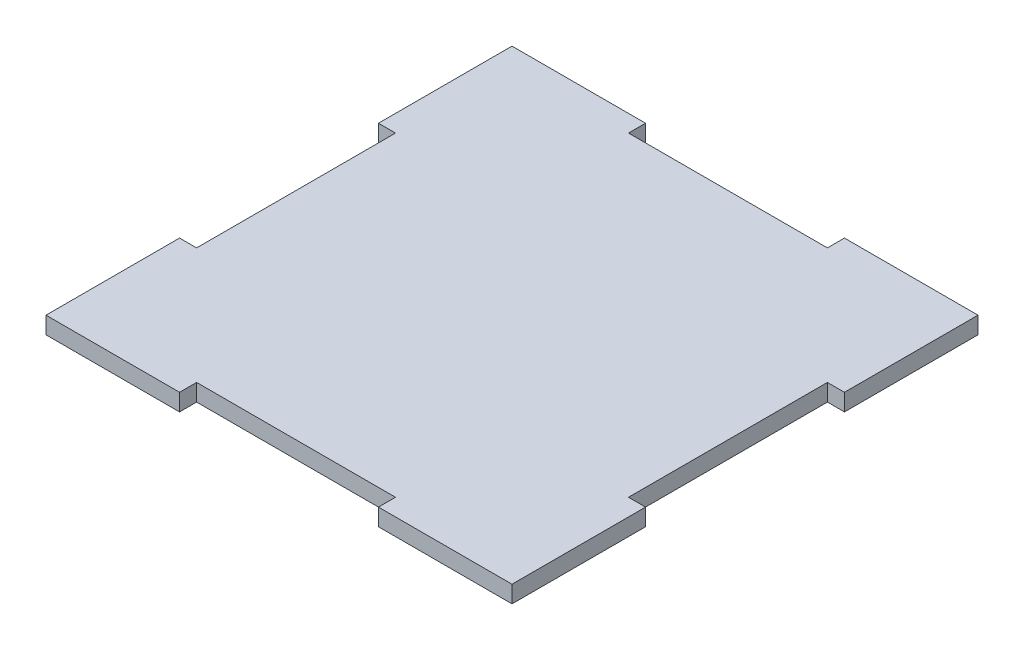
SolidWorks part; units mm, degrees
ref_plane "Front Plane" through (0, 0, 0) normal (0, 0, 1) x (1, 0, 0)
ref_plane "Top Plane" through (0, 0, 0) normal (0, 1, 0) x (1, 0, 0)
ref_plane "Right Plane" through (0, 0, 0) normal (1, 0, 0) x (0, 0, -1)
sketch "Sketch1" plane through (0, 0, 0) normal (0, 1, 0) x (1, 0, 0)
  line L0 (0, 38) -> (0, -38) construction
  line L1 (-41, -41) -> (-17.5, -41)
  line L2 (-41, -41) -> (-41, -17.5)
  line L3 (-41, 41) -> (-17.5, 41)
  line L4 (41, -41) -> (41, -17.5)
  line L5 (-41, -41) -> (41, 41) construction
  line L6 (-41, 41) -> (41, -41) construction
  line L11 (-41, 17.5) -> (-38, 17.5)
  line L12 (-38, 17.5) -> (-38, -17.5)
  line L13 (-35, 0) -> (38, 0) construction
  line L26 (17.5, 41) -> (41, 41)
  line L27 (41, 17.5) -> (41, 41)
  line L28 (17.5, -41) -> (41, -41)
  line L29 (-41, 17.5) -> (-41, 41)
  line L30 (-38, -17.5) -> (-41, -17.5)
  line L31 (-17.5, 41) -> (-17.5, 38)
  line L32 (-17.5, 38) -> (17.5, 38)
  line L33 (17.5, 38) -> (17.5, 41)
  line L34 (41, 17.5) -> (38, 17.5)
  line L35 (38, 17.5) -> (38, -17.5)
  line L36 (38, -17.5) -> (41, -17.5)
  line L37 (17.5, -41) -> (17.5, -38)
  line L38 (17.5, -38) -> (-17.5, -38)
  line L39 (-17.5, -38) -> (-17.5, -41)
  point P0 (0, 0)
  point P6 (0, 0)
  dimension "D1" = 3
  dimension "D2" = 82
  dimension "D3" = 3
  dimension "D4" = 82
  dimension "D5" = 3
  dimension "D6" = 3
extrude "Boss-Extrude1" add sketch "Sketch1" along normal blind 3
